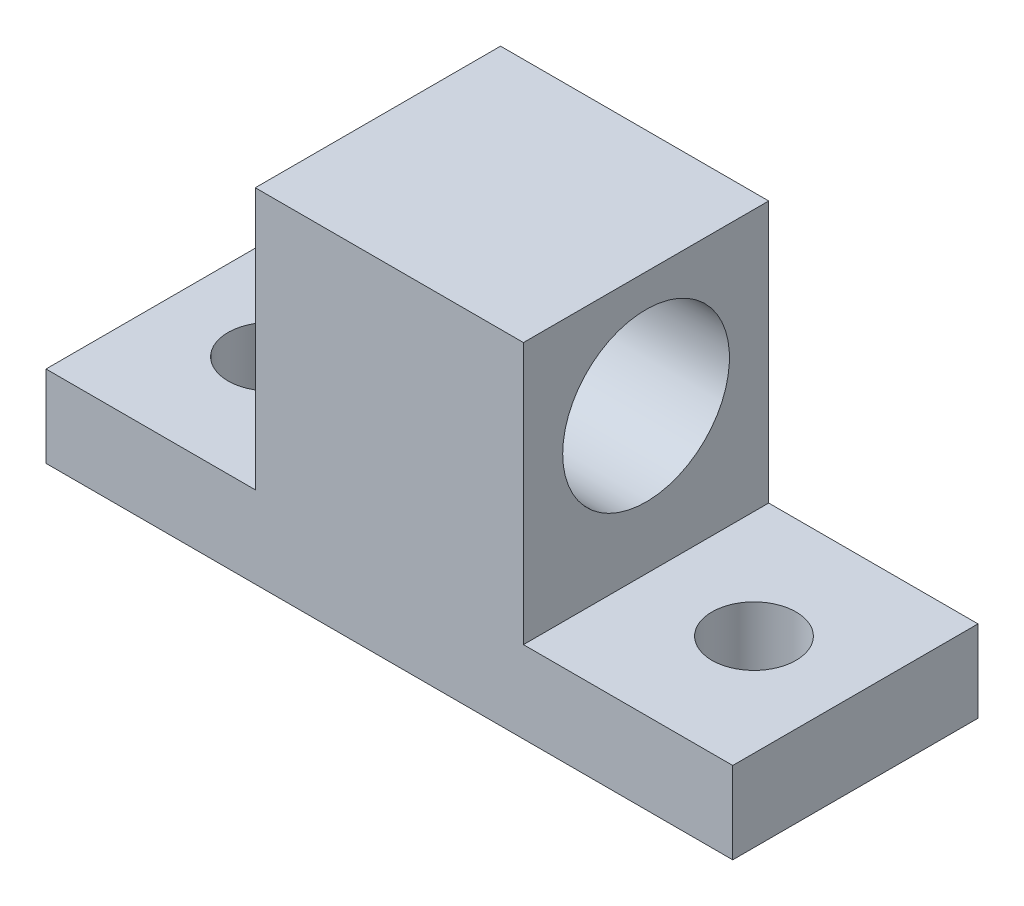
SolidWorks part; units mm, degrees
ref_plane "Front Plane" through (0, 0, 0) normal (0, 0, 1) x (1, 0, 0)
ref_plane "Top Plane" through (0, 0, 0) normal (0, 1, 0) x (1, 0, 0)
ref_plane "Right Plane" through (0, 0, 0) normal (1, 0, 0) x (0, 0, -1)
sketch "Sketch1" plane through (0, 0, 0) normal (0, 1, 0) x (1, 0, 0)
  line L1 (-35.381, 3.1139) -> (17.959, 3.1139)
  line L2 (-35.381, 3.1139) -> (-35.381, -15.9361)
  line L3 (-35.381, -15.9361) -> (17.959, -15.9361)
  line L4 (17.959, 3.1139) -> (17.959, -15.9361)
  line L5 (-19.887, 3.1139) -> (2.465, 3.1139)
  line L6 (-19.887, 3.1139) -> (-19.887, -15.9361)
  line L7 (-19.887, -15.9361) -> (2.465, -15.9361)
  line L8 (2.465, 3.1139) -> (2.465, -15.9361)
  circle A0 centre (-27.507, -6.4111) radius 3.2639
  circle A1 centre (10.085, -6.4111) radius 3.2639
  dimension "D7" = 6.5278
  dimension "D8" = 6.5278
  dimension "D1" = 19.05
  dimension "D2" = 53.34
  dimension "D3" = 7.874
  dimension "D4" = 7.874
  dimension "D5" = 9.525
  dimension "D6" = 9.525
  dimension "D9" = 7.62
  dimension "D10" = 7.62
extrude "Boss-Extrude3" add sketch "Sketch1" along normal blind 6.35 contours L6 L1 L2 L3 A0 | L8 L1 L6 L3 | L1 L8 L3 L4 A1
sketch "Sketch3" plane through (0, 6.35, 0) normal (0, 1, 0) x (1, 0, 0)
  line L0 (-35.381, -15.9361) -> (17.959, -15.9361) construction
  line L1 (-19.125, -15.9361) -> (1.703, -15.9361)
  line L2 (-19.125, -15.9361) -> (-19.125, 3.1139)
  line L3 (-19.125, 3.1139) -> (1.703, 3.1139)
  line L4 (1.703, -15.9361) -> (1.703, 3.1139)
  line L5 (-35.381, 3.1139) -> (17.959, 3.1139) construction
  circle A0 centre (-27.507, -6.4111) radius 3.2639 construction
  circle A1 centre (10.085, -6.4111) radius 3.2639 construction
  dimension "D1" = 8.382
  dimension "D2" = 8.382
extrude "Boss-Extrude4" add sketch "Sketch3" along normal blind 20.32
sketch "Sketch4" plane through (-19.125, 0, 0) normal (-1, 0, 0) x (0, 0, 1)
  line L0 (15.9361, 26.67) -> (15.9361, 6.35) construction
  line L1 (-3.1139, 26.67) -> (15.9361, 26.67) construction
  circle A0 centre (6.4111, 17.6563) radius 6.477
  point P2 (15.9361, 16.51)
  dimension "D3" = 12.954
  dimension "D1" = 9.525
  dimension "D2" = 9.0137
extrude "Cut-Extrude1" cut sketch "Sketch4" against normal up to next
